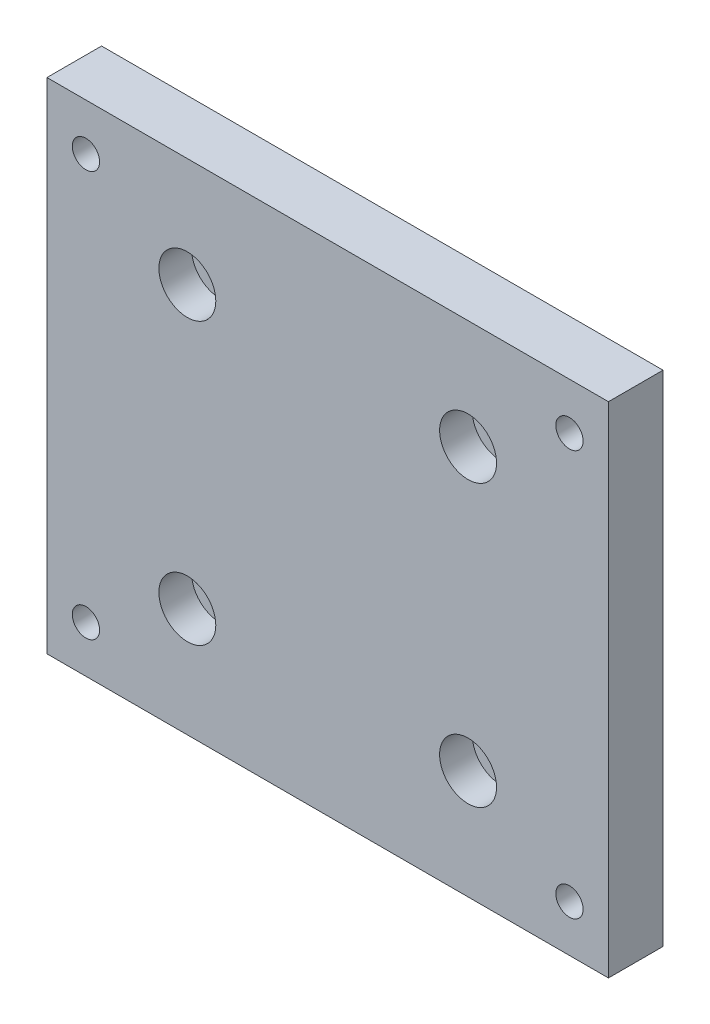
SolidWorks part; units mm, degrees
ref_plane "前基準面" through (0, 0, 0) normal (0, 0, 1) x (1, 0, 0)
ref_plane "上基準面" through (0, 0, 0) normal (0, 1, 0) x (1, 0, 0)
ref_plane "右基準面" through (0, 0, 0) normal (1, 0, 0) x (0, 0, -1)
sketch "草圖2" plane through (0, 0, 0) normal (0, 0, 1) x (1, 0, 0)
  line L0 (0, 0) -> (0, 30.0174) construction
  line L1 (-36, 32) -> (36, 32)
  line L2 (-36, 32) -> (-36, -32)
  line L3 (-36, -32) -> (36, -32)
  line L4 (36, 32) -> (36, -32)
  line L5 (-36, 32) -> (36, -32) construction
  line L6 (-36, -32) -> (36, 32) construction
  line L7 (0, -5.5) -> (0, 5.5) construction
  line L8 (0, 0) -> (-44.8344, 0) construction
  line L9 (5.5, 0) -> (-5.5, 0) construction
  line L10 (57, 0) -> (12.1656, 0) construction
  line L11 (57, -36) -> (12.1656, -36) construction
  line L12 (0, -36) -> (-44.8344, -36) construction
  circle A0 centre (-18, 18) radius 2.25
  circle A1 centre (-31, 26) radius 1.75
  circle A2 centre (18, 18) radius 2.25
  circle A3 centre (18, -18) radius 2.25
  circle A4 centre (-18, -18) radius 2.25
  circle A8 centre (31, 26) radius 1.75
  circle A9 centre (31, -26) radius 1.75
  circle A10 centre (-31, -26) radius 1.75
  point P0 (0, 0)
  dimension "D3" = 4.5
  dimension "D6" = 3.5
  dimension "D9" = 31
  dimension "D10" = 26
  dimension "D1" = 72
  dimension "D2" = 64
  dimension "D4" = 36
  dimension "D5" = 36
extrude "填料-伸長1" add sketch "草圖2" along normal blind 7
hole_wizard "鑽孔1" positions "3D草圖1" profile "草圖3" legacy end condition through all
sketch3d "3D草圖1"
  line L0 (-18, 18, 7) -> (-18, 18, 0) construction
  line L1 (18, 18, 7) -> (18, 18, 0) construction
  line L2 (18, -18, 7) -> (18, -18, 0) construction
  line L3 (-18, -18, 7) -> (-18, -18, 0) construction
  point P0 (-18, 18, 7)
  point P4 (18, 18, 7)
  point P8 (18, -18, 7)
  point P12 (-18, -18, 7)
sketch "草圖3" plane through (-18, 18, 7) normal (1, 0, 0) x (0, -1, 0)
  line L0 (0, 0) -> (0, 7)
  line L1 (0, 7) -> (2.25, 7)
  line L2 (2.25, 7) -> (2.25, 4.2)
  line L3 (2.25, 4.2) -> (3.65, 4.2)
  line L4 (3.65, 4.2) -> (3.65, 0)
  line L5 (3.65, 0) -> (0, 0)
  line L6 (0, 110) -> (0, -10) construction
  dimension "直徑" = 4.5
  dimension "深度" = 7
  dimension "柱孔直徑1" = 7.3
  dimension "柱孔深度1" = 4.2
sketch "草圖4" plane through (0, 0, 0) normal (0, 0, -1) x (-1, 0, 0)
  line L0 (0, 5.5) -> (0, -5.5) construction
  line L1 (-27.7091, 26) -> (-29.3546, 28.85)
  line L2 (-29.3546, 28.85) -> (-32.6454, 28.85)
  line L3 (-32.6454, 28.85) -> (-34.2909, 26)
  line L4 (-34.2909, 26) -> (-32.6454, 23.15)
  line L5 (-32.6454, 23.15) -> (-29.3546, 23.15)
  line L6 (-29.3546, 23.15) -> (-27.7091, 26)
  line L25 (29.3546, 23.15) -> (27.7091, 26)
  line L26 (32.6454, 23.15) -> (29.3546, 23.15)
  line L27 (34.2909, 26) -> (32.6454, 23.15)
  line L28 (32.6454, 28.85) -> (34.2909, 26)
  line L29 (29.3546, 28.85) -> (32.6454, 28.85)
  line L30 (27.7091, 26) -> (29.3546, 28.85)
  line L31 (5.5, 0) -> (-5.5, 0) construction
  line L32 (27.7091, -26) -> (29.3546, -28.85)
  line L33 (29.3546, -28.85) -> (32.6454, -28.85)
  line L34 (32.6454, -28.85) -> (34.2909, -26)
  line L35 (34.2909, -26) -> (32.6454, -23.15)
  line L36 (32.6454, -23.15) -> (29.3546, -23.15)
  line L37 (29.3546, -23.15) -> (27.7091, -26)
  line L38 (-29.3546, -23.15) -> (-27.7091, -26)
  line L39 (-32.6454, -23.15) -> (-29.3546, -23.15)
  line L40 (-34.2909, -26) -> (-32.6454, -23.15)
  line L41 (-32.6454, -28.85) -> (-34.2909, -26)
  line L42 (-29.3546, -28.85) -> (-32.6454, -28.85)
  line L43 (-27.7091, -26) -> (-29.3546, -28.85)
  circle A0 centre (-31, 26) radius 2.85 construction
  circle A1 centre (31, 26) radius 2.85 construction
  circle A2 centre (31, -26) radius 2.85 construction
  circle A3 centre (-31, -26) radius 2.85 construction
  dimension "D1" = 5.7
extrude "除料-伸長1" cut sketch "草圖4" against normal blind 2.5
